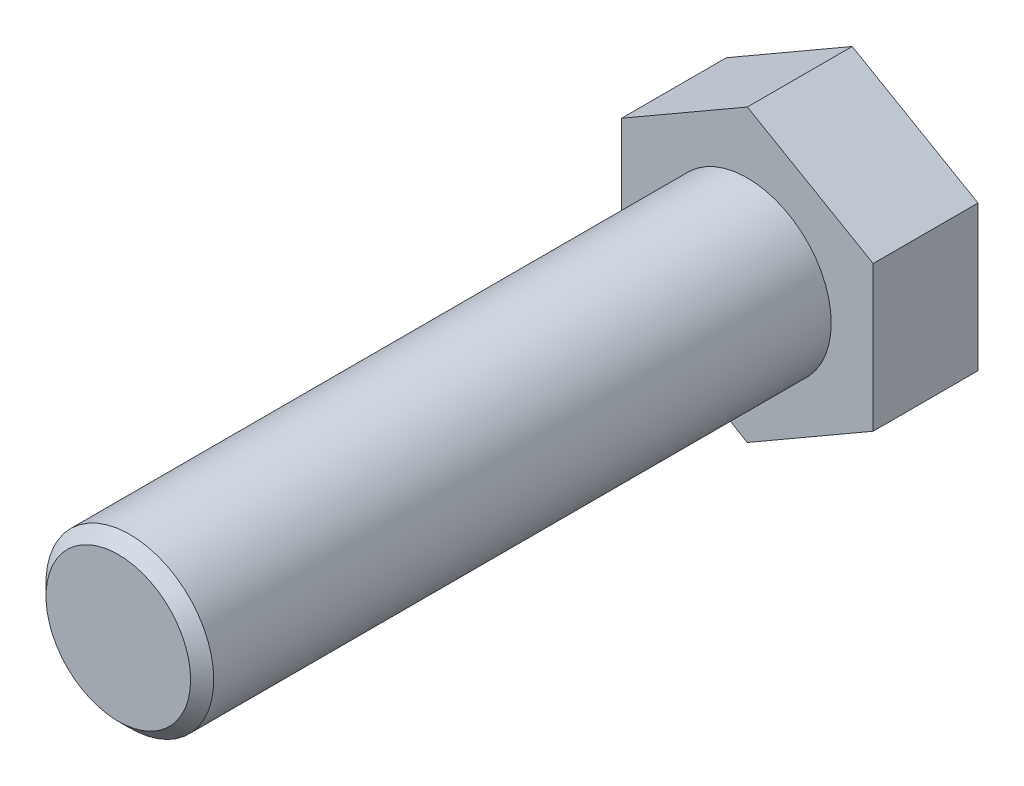
SolidWorks part; units mm, degrees
material "Сталь"
ref_plane "Спереди" through (0, 0, 0) normal (0, 0, 1) x (1, 0, 0)
ref_plane "Сверху" through (0, 0, 0) normal (0, 1, 0) x (1, 0, 0)
ref_plane "Справа" through (0, 0, 0) normal (1, 0, 0) x (0, 0, -1)
sketch "Эскиз1" plane through (0, 0, 0) normal (0, 0, 1) x (1, 0, 0)
  line L1 (0, 10.3923) -> (-9, 5.1962)
  line L2 (-9, 5.1962) -> (-9, -5.1962)
  line L3 (-9, -5.1962) -> (0, -10.3923)
  line L4 (0, -10.3923) -> (9, -5.1962)
  line L5 (9, -5.1962) -> (9, 5.1962)
  line L6 (9, 5.1962) -> (0, 10.3923)
  circle A0 centre (0, 0) radius 9 construction
  dimension "D1" = 18
extrude "Бобышка-Вытянуть1" add sketch "Эскиз1" along normal blind 7.5
sketch "Эскиз2" plane through (0, 0, 7.5) normal (0, 0, 1) x (1, 0, 0)
  circle A0 centre (0, 0) radius 6
  dimension "D1" = 12
extrude "Бобышка-Вытянуть2" add sketch "Эскиз2" along normal blind 45
cosmetic thread "Условное изображение резьбы1" parameters "D1"=35, "D2"=10.344
chamfer "Фаска1" distance 0.828 angle 45 1 edges at (6, 0, 52.5)
